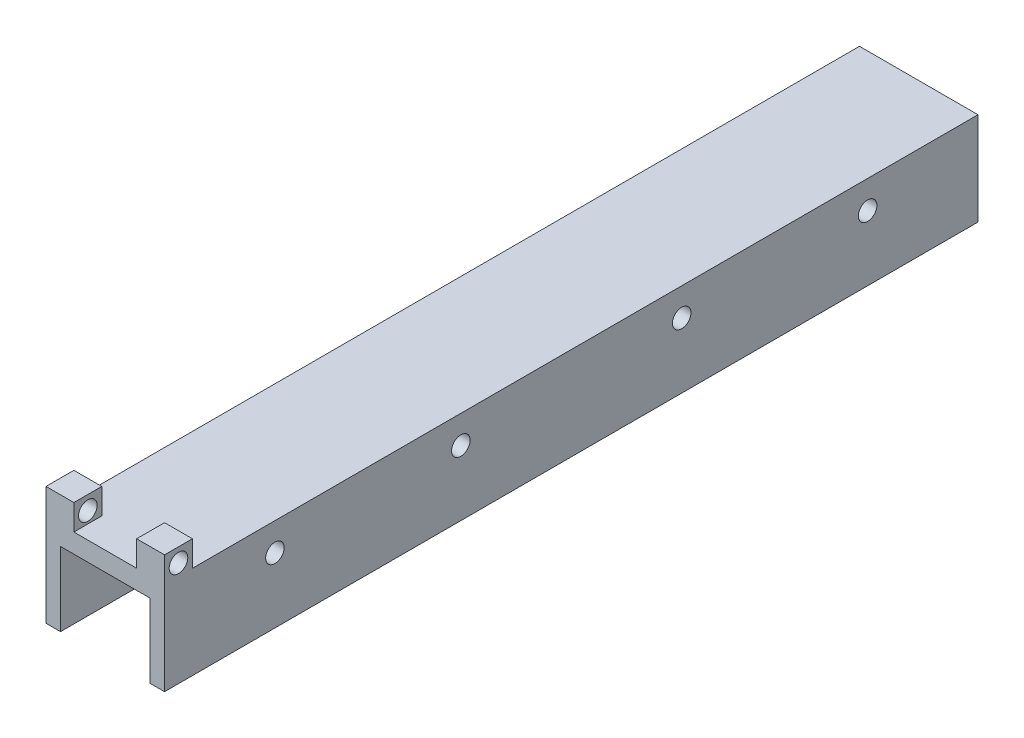
SolidWorks part; units mm, degrees
ref_plane "Front Plane" through (0, 0, 0) normal (0, 0, 1) x (1, 0, 0)
ref_plane "Top Plane" through (0, 0, 0) normal (0, 1, 0) x (1, 0, 0)
ref_plane "Right Plane" through (0, 0, 0) normal (1, 0, 0) x (0, 0, -1)
sketch "Sketch2" plane through (0, 0, 0) normal (0, 0, 1) x (1, 0, 0)
  line L0 (319.8414, 0) -> (-319.8414, 0) construction
  line L2 (0, 0) -> (0, 20.32)
  line L3 (0, 20.32) -> (25.908, 20.32)
  line L4 (25.908, 0) -> (25.908, 20.32)
  line L44 (22.733, 16.129) -> (22.733, 0)
  line L47 (3.175, 0) -> (3.175, 16.129)
  line L48 (3.175, 16.129) -> (22.733, 16.129)
  line L49 (0, 0) -> (3.175, 0)
  line L50 (22.733, 0) -> (25.908, 0)
  dimension "D1" = 20.32
  dimension "D2" = 25.908
  dimension "D3" = 3.175
  dimension "D4" = 19.558
  dimension "D5" = 3.175
  dimension "D7" = 16.129
extrude "Boss-Extrude2" add sketch "Sketch2" against normal blind 177.8
sketch "Sketch19" plane through (0, 0, 0) normal (1, 0, 0) x (0, 0, -1)
  line L0 (0, 265.0009) -> (0, -265.0009) construction
  line L1 (319.8414, 0) -> (-319.8414, 0) construction
  line L3 (0, 0) -> (88.9, 0) construction
  line L4 (177.8, 0) -> (0, 0) construction
  line L5 (88.9, 0) -> (88.9, 20.32) construction
  line L6 (177.8, 20.32) -> (0, 20.32) construction
  line L7 (177.8, 0) -> (177.8, 20.32) construction
  circle A0 centre (24.13, 14.224) radius 2.032
  circle A1 centre (64.77, 14.224) radius 2.032
  circle A2 centre (113.03, 14.224) radius 2.032
  circle A3 centre (153.67, 14.224) radius 2.032
  dimension "D2" = 4.064
  dimension "D5" = 4.064
  dimension "D9" = 24.13
  dimension "D1" = 24.13
  dimension "D3" = 14.224
  dimension "D4" = 40.64
  dimension "D6" = 14.224
  dimension "D7" = 24.13
  dimension "D8" = 88.9
  dimension "D10" = 40.64
  dimension "D11" = 24.13
extrude "Cut-Extrude3" cut sketch "Sketch19" along normal through all
sketch "Sketch20" plane through (25.908, 0, 0) normal (1, 0, 0) x (0, 0, -1)
sketch "Sketch21" plane through (0, 20.32, 0) normal (0, 1, 0) x (1, 0, 0)
  line L0 (12.954, 0) -> (12.954, 177.8) construction
  line L1 (0, 0) -> (25.908, 0) construction
  line L2 (0, 0) -> (6.096, 0)
  line L3 (0, 0) -> (0, 6.096)
  line L4 (0, 6.096) -> (6.096, 6.096)
  line L5 (6.096, 0) -> (6.096, 6.096)
  line L6 (25.908, 177.8) -> (0, 177.8) construction
  line L7 (0, 0) -> (6.096, 0) construction
  line L8 (6.096, 0) -> (6.096, 6.5548) construction
  line L10 (19.812, 0) -> (19.812, 6.5548) construction
  line L11 (25.908, 0) -> (19.812, 0)
  line L12 (25.908, 0) -> (25.908, 6.096)
  line L13 (25.908, 6.096) -> (19.812, 6.096)
  line L14 (19.812, 0) -> (19.812, 6.096)
  dimension "D1" = 6.096
  dimension "D2" = 6.096
  dimension "D3" = 6.096
  dimension "D4" = 13.716
  dimension "D5" = 6.096
  dimension "D6" = 6.096
  dimension "D7" = 6.096
extrude "Boss-Extrude4" add sketch "Sketch21" along normal blind 5.588
sketch "Sketch22" plane through (19.812, 0, 0) normal (-1, 0, 0) x (0, 0, 1)
  line L0 (0, 25.908) -> (-6.096, 25.908) construction
  line L1 (0, -265.0009) -> (0, 265.0009) construction
  circle A0 centre (-3.048, 22.86) radius 2.032
  point P4 (-3.048, 25.908)
  dimension "D1" = 4.064
  dimension "D2" = 3.048
  dimension "D3" = 3.048
extrude "Cut-Extrude4" cut sketch "Sketch22" against normal through all both and the other way through all
